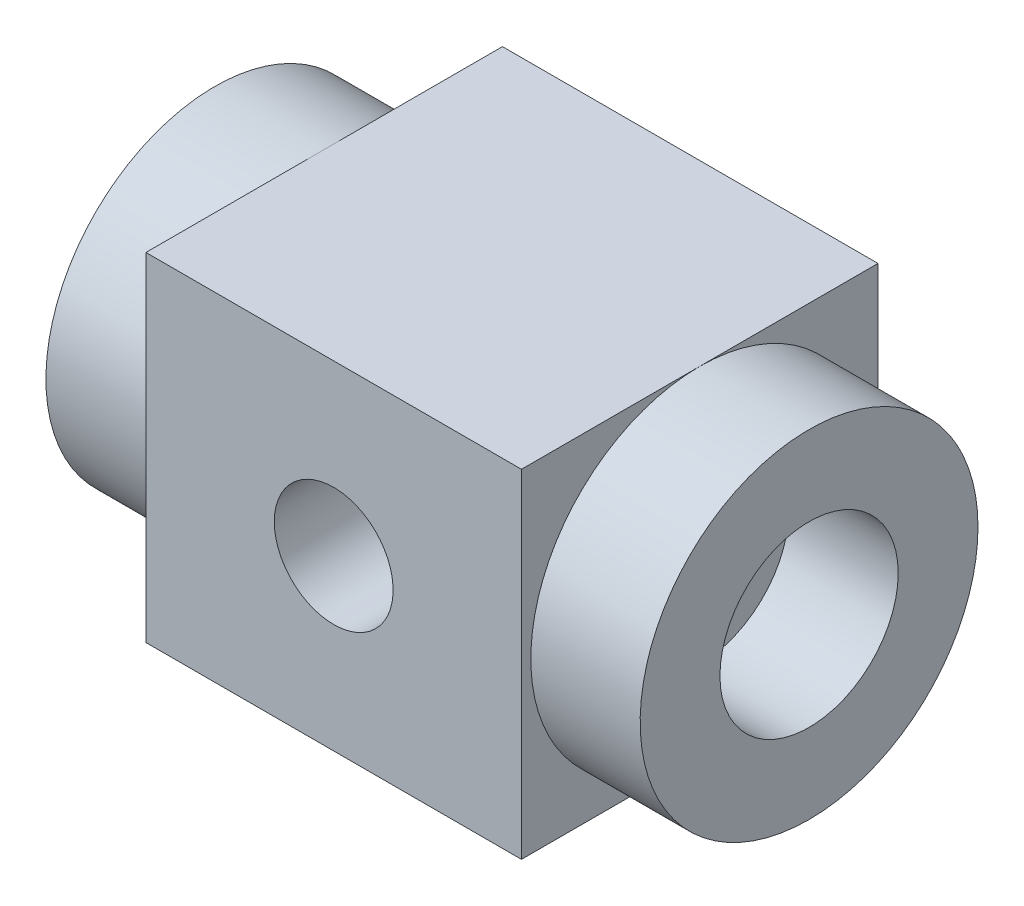
SolidWorks part; units mm, degrees
ref_plane "Front Plane" through (0, 0, 0) normal (0, 0, 1) x (1, 0, 0)
ref_plane "Top Plane" through (0, 0, 0) normal (0, 1, 0) x (1, 0, 0)
ref_plane "Right Plane" through (0, 0, 0) normal (1, 0, 0) x (0, 0, -1)
sketch "Sketch1" plane through (0, 0, 0) normal (0, 0, 1) x (1, 0, 0)
  line L1 (-15.8, -14.214) -> (15.8, -14.214)
  line L2 (-15.8, -14.214) -> (-15.8, 14.214)
  line L3 (-15.8, 14.214) -> (15.8, 14.214)
  line L4 (15.8, -14.214) -> (15.8, 14.214)
  line L5 (-15.8, -14.214) -> (15.8, 14.214) construction
  line L6 (-15.8, 14.214) -> (15.8, -14.214) construction
  point P0 (0, 0)
  dimension "D1" = 31.6
extrude "Boss-Extrude1" add sketch "Sketch1" along normal blind 30
sketch "Sketch2" plane through (0, 0, 0) normal (1, 0, 0) x (0, 0, -1)
  line L0 (-30, 0) -> (0, 0) construction
  line L1 (-30, -14.214) -> (-30, 14.214) construction
  circle A0 centre (-15, 0) radius 14.214
extrude "Boss-Extrude2" add sketch "Sketch2" along normal mid plane 50
sketch "Sketch3" plane through (25, 0, 0) normal (1, 0, 0) x (0, 0, -1)
  line L0 (-29.214, 0) -> (-0.786, 0) construction
  circle A0 centre (-15, 0) radius 14.214 construction
  circle A1 centre (-15, 0) radius 7.5
  dimension "D1" = 15
extrude "Cut-Extrude1" cut sketch "Sketch3" against normal blind 75
sketch "Sketch4" plane through (0, 0, 0) normal (0, 0, -1) x (-1, 0, 0)
  line L0 (0, 14.214) -> (0, -14.214) construction
  line L1 (-15.8, 14.214) -> (15.8, 14.214) construction
  line L2 (15.8, -14.214) -> (-15.8, -14.214) construction
  circle A0 centre (0, 0) radius 5
  dimension "D1" = 10
extrude "Cut-Extrude2" cut sketch "Sketch4" against normal blind 75
sketch "Sketch5" plane through (0, 14.214, 0) normal (0, 1, 0) x (1, 0, 0)
  line L0 (15.8, -30) -> (-15.8, -30) construction
  line L1 (-15.8, 0) -> (-11.097, 0)
  line L2 (-15.8, 0) -> (-15.8, -30)
  line L3 (-15.8, -30) -> (-11.097, -30)
  line L4 (-11.097, 0) -> (-11.097, -30)
  line L5 (15.8, 0) -> (-15.8, 0) construction
  line L6 (15.8, -30) -> (11.1069, -30)
  line L7 (15.8, -30) -> (15.8, 0)
  line L8 (15.8, 0) -> (11.1069, 0)
  line L9 (11.1069, -30) -> (11.1069, 0)
extrude "Boss-Extrude3" add sketch "Sketch5" against normal through all
